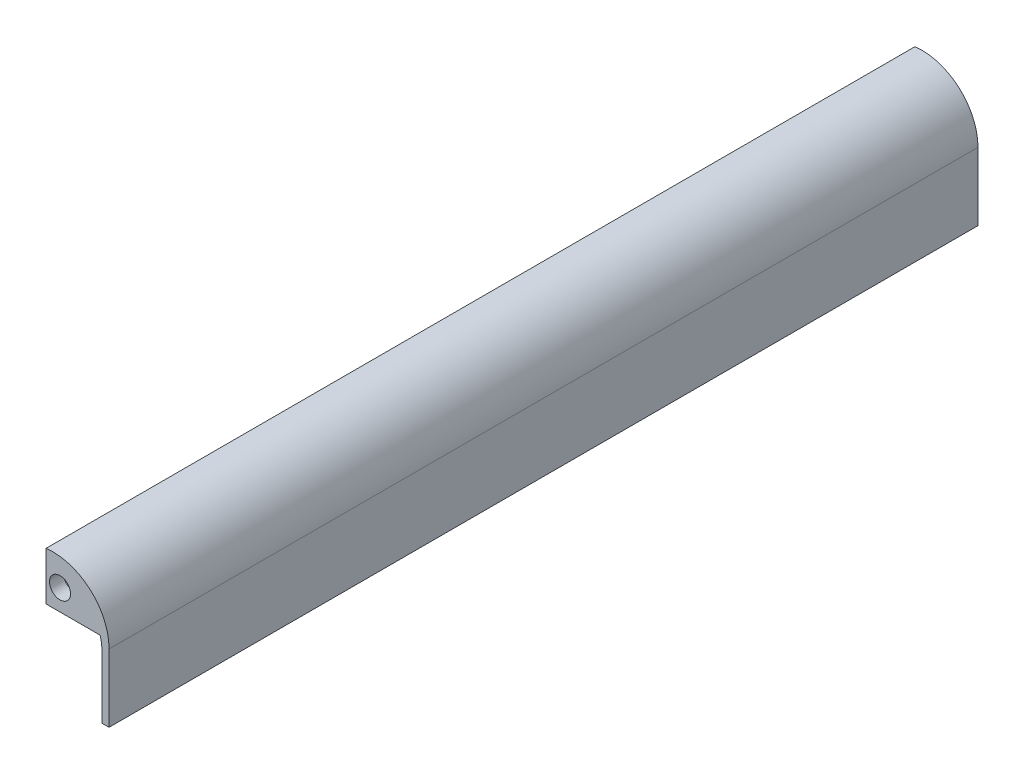
SolidWorks part; units mm, degrees
ref_plane "Front Plane" through (0, 0, 0) normal (0, 0, 1) x (1, 0, 0)
ref_plane "Top Plane" through (0, 0, 0) normal (0, 1, 0) x (1, 0, 0)
ref_plane "Right Plane" through (0, 0, 0) normal (1, 0, 0) x (0, 0, -1)
sketch "Sketch1" plane through (0, 0, 0) normal (0, 0, 1) x (1, 0, 0)
  line L0 (0, 0) -> (12.7, 0)
  line L1 (0, 0) -> (0, -12.7)
  line L2 (101.6, -114.3) -> (101.6, -224.5508)
  line L3 (101.6, -224.5508) -> (114.3, -224.5508)
  line L4 (114.3, -224.5508) -> (114.3, -101.6)
  arc A0 (114.3, -101.6) -> (0, -0.7969) centre (12.7, -101.6) ccw
  arc A1 (101.6, -114.3) -> (0, -12.7) centre (0, -114.3) ccw
  dimension "D1" = 203.2
  dimension "D4" = 203.2
  dimension "D2" = 12.7
  dimension "D3" = 12.7
  dimension "D5" = 12.7
extrude "Boss-Extrude1" add sketch "Sketch1" along normal blind 1574.8 contours A1 L2 L3 L4 A0 L1
sketch "Sketch2" plane through (0, 0, 0) normal (0, 0, -1) x (-1, 0, 0)
  line L0 (0, -0.7969) -> (0, -88.0325)
  line L1 (0, -88.0325) -> (-113.39, -88.0325)
  arc A0 (0, -0.7969) -> (-114.3, -101.6) centre (-12.7, -101.6) ccw construction
  arc A1 (-113.39, -88.0325) -> (0, -0.7969) centre (-12.7, -101.6) cw
extrude "Boss-Extrude2" add sketch "Sketch2" against normal blind 25.4
ref_plane "Plane1" through (0, 0, 787.4) normal (0, 0, -1) x (-1, 0, 0)
mirror "Mirror2" about plane through (0, 0, 787.4) normal (0, 0, -1) of "Boss-Extrude2"
sketch "Sketch3" plane through (0, 0, 0) normal (0, 0, -1) x (-1, 0, 0)
  line L0 (-98.1457, -88.0325) -> (0, -88.0325) construction
  line L1 (0, -0.7969) -> (0, -88.0325) construction
  circle A0 centre (-25.4, -49.9325) radius 19.05
  dimension "D1" = 38.1
  dimension "D2" = 38.1
  dimension "D3" = 25.4
extrude "Cut-Extrude1" cut sketch "Sketch3" against normal through all
